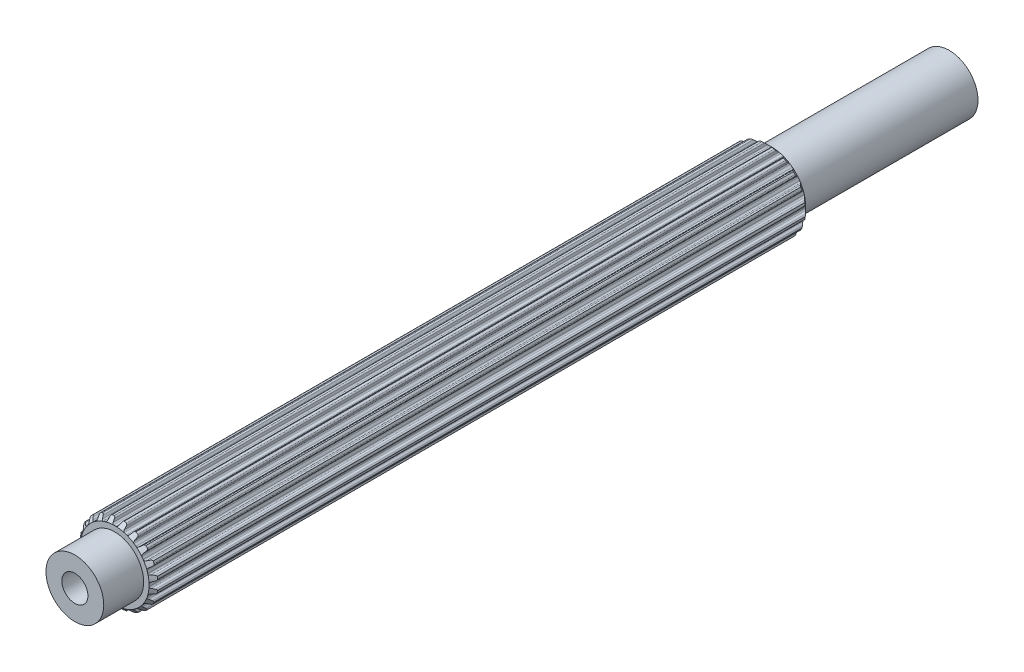
SolidWorks part; units mm, degrees
ref_plane "Front Plane" through (0, 0, 0) normal (0, 0, 1) x (1, 0, 0)
ref_plane "Top Plane" through (0, 0, 0) normal (0, 1, 0) x (1, 0, 0)
ref_plane "Right Plane" through (0, 0, 0) normal (1, 0, 0) x (0, 0, -1)
sketch "Sketch1" plane through (0, 0, 0) normal (0, 0, 1) x (1, 0, 0)
  line L0 (-0.1069, 2.9699) -> (0.1069, 2.9699)
  line L1 (0.3159, 3.2375) -> (0.2537, 3.0575)
  line L2 (-0.2964, 3.2367) -> (-0.2318, 3.0575)
  line L3 (-0.2964, 3.2367) -> (0.3159, 3.2375) construction
  line L4 (0, 3.3252) -> (0, 0) construction
  line L5 (-0.2318, 3.0575) -> (0.2537, 3.0575) construction
  line L6 (-0.4281, 3.3241) -> (0.4281, 3.3263) construction
  line L7 (0.7183, 3.1698) -> (0.7244, 2.9795)
  line L8 (0.816, 2.8576) -> (1.0195, 2.7915)
  line L9 (1.3009, 2.9815) -> (1.1862, 2.8295)
  line L10 (1.6627, 2.7927) -> (1.6097, 2.6099)
  line L11 (1.6591, 2.4655) -> (1.8322, 2.3398)
  line L12 (2.1585, 2.4335) -> (2.0025, 2.3245)
  line L13 (2.4443, 2.1423) -> (2.3374, 1.9847)
  line L14 (2.3398, 1.8322) -> (2.4655, 1.6591)
  line L15 (2.8049, 1.6474) -> (2.6228, 1.5919)
  line L16 (2.9866, 1.2821) -> (2.8363, 1.1653)
  line L17 (2.7915, 1.0195) -> (2.8576, 0.816)
  line L18 (3.1767, 0.7) -> (2.9863, 0.7035)
  line L19 (3.2367, 0.2964) -> (3.0575, 0.2318)
  line L20 (2.9699, 0.1069) -> (2.9699, -0.1069)
  line L21 (3.2375, -0.3159) -> (3.0575, -0.2537)
  line L22 (3.1698, -0.7183) -> (2.9795, -0.7244)
  line L23 (2.8576, -0.816) -> (2.7915, -1.0195)
  line L24 (2.9815, -1.3009) -> (2.8295, -1.1862)
  line L25 (2.7927, -1.6627) -> (2.6099, -1.6097)
  line L26 (2.4655, -1.6591) -> (2.3398, -1.8322)
  line L27 (2.4335, -2.1585) -> (2.3245, -2.0025)
  line L28 (2.1423, -2.4443) -> (1.9847, -2.3374)
  line L29 (1.8322, -2.3398) -> (1.6591, -2.4655)
  line L30 (1.6474, -2.8049) -> (1.5919, -2.6228)
  line L31 (1.2821, -2.9866) -> (1.1653, -2.8363)
  line L32 (1.0195, -2.7915) -> (0.816, -2.8576)
  line L33 (0.7, -3.1767) -> (0.7035, -2.9863)
  line L34 (0.2964, -3.2367) -> (0.2318, -3.0575)
  line L35 (0.1069, -2.9699) -> (-0.1069, -2.9699)
  line L36 (-0.3159, -3.2375) -> (-0.2537, -3.0575)
  line L37 (-0.7183, -3.1698) -> (-0.7244, -2.9795)
  line L38 (-0.816, -2.8576) -> (-1.0195, -2.7915)
  line L39 (-1.3009, -2.9815) -> (-1.1862, -2.8295)
  line L40 (-1.6627, -2.7927) -> (-1.6097, -2.6099)
  line L41 (-1.6591, -2.4655) -> (-1.8322, -2.3398)
  line L42 (-2.1585, -2.4335) -> (-2.0025, -2.3245)
  line L43 (-2.4443, -2.1423) -> (-2.3374, -1.9847)
  line L44 (-2.3398, -1.8322) -> (-2.4655, -1.6591)
  line L45 (-2.8049, -1.6474) -> (-2.6228, -1.5919)
  line L46 (-2.9866, -1.2821) -> (-2.8363, -1.1653)
  line L47 (-2.7915, -1.0195) -> (-2.8576, -0.816)
  line L48 (-3.1767, -0.7) -> (-2.9863, -0.7035)
  line L49 (-3.2367, -0.2964) -> (-3.0575, -0.2318)
  line L50 (-2.9699, -0.1069) -> (-2.9699, 0.1069)
  line L51 (-3.2375, 0.3159) -> (-3.0575, 0.2537)
  line L52 (-3.1698, 0.7183) -> (-2.9795, 0.7244)
  line L53 (-2.8576, 0.816) -> (-2.7915, 1.0195)
  line L54 (-2.9815, 1.3009) -> (-2.8295, 1.1862)
  line L55 (-2.7927, 1.6627) -> (-2.6099, 1.6097)
  line L56 (-2.4655, 1.6591) -> (-2.3398, 1.8322)
  line L57 (-2.4335, 2.1585) -> (-2.3245, 2.0025)
  line L58 (-2.1423, 2.4443) -> (-1.9847, 2.3374)
  line L59 (-1.8322, 2.3398) -> (-1.6591, 2.4655)
  line L60 (-1.6474, 2.8049) -> (-1.5919, 2.6228)
  line L61 (-1.2821, 2.9866) -> (-1.1653, 2.8363)
  line L62 (-1.0195, 2.7915) -> (-0.816, 2.8576)
  line L63 (-0.7, 3.1767) -> (-0.7035, 2.9863)
  line L64 (0.4281, 3.3263) -> (0.62, 3.2938)
  line L65 (1.4351, 3.0312) -> (1.6075, 2.9409)
  line L66 (2.3015, 2.4394) -> (2.4376, 2.3003)
  line L67 (2.9427, 1.6088) -> (3.0291, 1.4344)
  line L68 (3.2958, 0.6207) -> (3.3241, 0.4281)
  line L69 (3.3263, -0.4281) -> (3.2938, -0.62)
  line L70 (3.0312, -1.4351) -> (2.9409, -1.6075)
  line L71 (2.4394, -2.3015) -> (2.3003, -2.4376)
  line L72 (1.6088, -2.9427) -> (1.4344, -3.0291)
  line L73 (0.6207, -3.2958) -> (0.4281, -3.3241)
  line L74 (-0.4281, -3.3263) -> (-0.62, -3.2938)
  line L75 (-1.4351, -3.0312) -> (-1.6075, -2.9409)
  line L76 (-2.3015, -2.4394) -> (-2.4376, -2.3003)
  line L77 (-2.9427, -1.6088) -> (-3.0291, -1.4344)
  line L78 (-3.2958, -0.6207) -> (-3.3241, -0.4281)
  line L79 (-3.3263, 0.4281) -> (-3.2938, 0.62)
  line L80 (-3.0312, 1.4351) -> (-2.9409, 1.6075)
  line L81 (-2.4394, 2.3015) -> (-2.3003, 2.4376)
  line L82 (-1.6088, 2.9427) -> (-1.4344, 3.0291)
  line L83 (-0.6207, 3.2958) -> (-0.4281, 3.3241)
  arc A0 (0.2537, 3.0575) -> (0.1069, 2.9699) centre (0.1283, 3.1009) cw
  arc A1 (-0.2318, 3.0575) -> (-0.1069, 2.9699) centre (-0.1069, 3.1026) ccw
  arc A2 (0.62, 3.2938) -> (0.7183, 3.1698) centre (0.5856, 3.1656) cw
  arc A3 (0.7244, 2.9795) -> (0.816, 2.8576) centre (0.857, 2.9838) ccw
  arc A4 (-0.4281, 3.3241) -> (-0.2964, 3.2367) centre (-0.4213, 3.1916) cw
  arc A5 (0.4281, 3.3263) -> (0.3159, 3.2375) centre (0.4413, 3.1942) ccw
  arc A6 (1.1862, 2.8295) -> (1.0195, 2.7915) centre (1.0802, 2.9095) cw
  arc A7 (1.4351, 3.0312) -> (1.3009, 2.9815) centre (1.4068, 2.9015) ccw
  arc A8 (1.6075, 2.9409) -> (1.6627, 2.7927) centre (1.5352, 2.8297) cw
  arc A9 (1.6097, 2.6099) -> (1.6591, 2.4655) centre (1.7371, 2.5729) ccw
  arc A10 (2.0025, 2.3245) -> (1.8322, 2.3398) centre (1.9264, 2.4332) cw
  arc A11 (2.3015, 2.4394) -> (2.1585, 2.4335) centre (2.2346, 2.3248) ccw
  arc A12 (2.4376, 2.3003) -> (2.4443, 2.1423) centre (2.3345, 2.2168) cw
  arc A13 (2.3374, 1.9847) -> (2.3398, 1.8322) centre (2.4472, 1.9102) ccw
  arc A14 (2.6228, 1.5919) -> (2.4655, 1.6591) centre (2.5841, 1.7189) cw
  arc A15 (2.9427, 1.6088) -> (2.8049, 1.6474) centre (2.8436, 1.5205) ccw
  arc A16 (3.0291, 1.4344) -> (2.9866, 1.2821) centre (2.9052, 1.3869) cw
  arc A17 (2.8363, 1.1653) -> (2.7915, 1.0195) centre (2.9177, 1.0605) ccw
  arc A18 (2.9863, 0.7035) -> (2.8576, 0.816) centre (2.9887, 0.8362) cw
  arc A19 (3.2958, 0.6207) -> (3.1767, 0.7) centre (3.1743, 0.5673) ccw
  arc A20 (3.3241, 0.4281) -> (3.2367, 0.2964) centre (3.1916, 0.4213) cw
  arc A21 (3.0575, 0.2318) -> (2.9699, 0.1069) centre (3.1026, 0.1069) ccw
  arc A22 (3.0575, -0.2537) -> (2.9699, -0.1069) centre (3.1009, -0.1283) cw
  arc A23 (3.3263, -0.4281) -> (3.2375, -0.3159) centre (3.1942, -0.4413) ccw
  arc A24 (3.2938, -0.62) -> (3.1698, -0.7183) centre (3.1656, -0.5856) cw
  arc A25 (2.9795, -0.7244) -> (2.8576, -0.816) centre (2.9838, -0.857) ccw
  arc A26 (2.8295, -1.1862) -> (2.7915, -1.0195) centre (2.9095, -1.0802) cw
  arc A27 (3.0312, -1.4351) -> (2.9815, -1.3009) centre (2.9015, -1.4068) ccw
  arc A28 (2.9409, -1.6075) -> (2.7927, -1.6627) centre (2.8297, -1.5352) cw
  arc A29 (2.6099, -1.6097) -> (2.4655, -1.6591) centre (2.5729, -1.7371) ccw
  arc A30 (2.3245, -2.0025) -> (2.3398, -1.8322) centre (2.4332, -1.9264) cw
  arc A31 (2.4394, -2.3015) -> (2.4335, -2.1585) centre (2.3248, -2.2346) ccw
  arc A32 (2.3003, -2.4376) -> (2.1423, -2.4443) centre (2.2168, -2.3345) cw
  arc A33 (1.9847, -2.3374) -> (1.8322, -2.3398) centre (1.9102, -2.4472) ccw
  arc A34 (1.5919, -2.6228) -> (1.6591, -2.4655) centre (1.7189, -2.5841) cw
  arc A35 (1.6088, -2.9427) -> (1.6474, -2.8049) centre (1.5205, -2.8436) ccw
  arc A36 (1.4344, -3.0291) -> (1.2821, -2.9866) centre (1.3869, -2.9052) cw
  arc A37 (1.1653, -2.8363) -> (1.0195, -2.7915) centre (1.0605, -2.9177) ccw
  arc A38 (0.7035, -2.9863) -> (0.816, -2.8576) centre (0.8362, -2.9887) cw
  arc A39 (0.6207, -3.2958) -> (0.7, -3.1767) centre (0.5673, -3.1743) ccw
  arc A40 (0.4281, -3.3241) -> (0.2964, -3.2367) centre (0.4213, -3.1916) cw
  arc A41 (0.2318, -3.0575) -> (0.1069, -2.9699) centre (0.1069, -3.1026) ccw
  arc A42 (-0.2537, -3.0575) -> (-0.1069, -2.9699) centre (-0.1283, -3.1009) cw
  arc A43 (-0.4281, -3.3263) -> (-0.3159, -3.2375) centre (-0.4413, -3.1942) ccw
  arc A44 (-0.62, -3.2938) -> (-0.7183, -3.1698) centre (-0.5856, -3.1656) cw
  arc A45 (-0.7244, -2.9795) -> (-0.816, -2.8576) centre (-0.857, -2.9838) ccw
  arc A46 (-1.1862, -2.8295) -> (-1.0195, -2.7915) centre (-1.0802, -2.9095) cw
  arc A47 (-1.4351, -3.0312) -> (-1.3009, -2.9815) centre (-1.4068, -2.9015) ccw
  arc A48 (-1.6075, -2.9409) -> (-1.6627, -2.7927) centre (-1.5352, -2.8297) cw
  arc A49 (-1.6097, -2.6099) -> (-1.6591, -2.4655) centre (-1.7371, -2.5729) ccw
  arc A50 (-2.0025, -2.3245) -> (-1.8322, -2.3398) centre (-1.9264, -2.4332) cw
  arc A51 (-2.3015, -2.4394) -> (-2.1585, -2.4335) centre (-2.2346, -2.3248) ccw
  arc A52 (-2.4376, -2.3003) -> (-2.4443, -2.1423) centre (-2.3345, -2.2168) cw
  arc A53 (-2.3374, -1.9847) -> (-2.3398, -1.8322) centre (-2.4472, -1.9102) ccw
  arc A54 (-2.6228, -1.5919) -> (-2.4655, -1.6591) centre (-2.5841, -1.7189) cw
  arc A55 (-2.9427, -1.6088) -> (-2.8049, -1.6474) centre (-2.8436, -1.5205) ccw
  arc A56 (-3.0291, -1.4344) -> (-2.9866, -1.2821) centre (-2.9052, -1.3869) cw
  arc A57 (-2.8363, -1.1653) -> (-2.7915, -1.0195) centre (-2.9177, -1.0605) ccw
  arc A58 (-2.9863, -0.7035) -> (-2.8576, -0.816) centre (-2.9887, -0.8362) cw
  arc A59 (-3.2958, -0.6207) -> (-3.1767, -0.7) centre (-3.1743, -0.5673) ccw
  arc A60 (-3.3241, -0.4281) -> (-3.2367, -0.2964) centre (-3.1916, -0.4213) cw
  arc A61 (-3.0575, -0.2318) -> (-2.9699, -0.1069) centre (-3.1026, -0.1069) ccw
  arc A62 (-3.0575, 0.2537) -> (-2.9699, 0.1069) centre (-3.1009, 0.1283) cw
  arc A63 (-3.3263, 0.4281) -> (-3.2375, 0.3159) centre (-3.1942, 0.4413) ccw
  arc A64 (-3.2938, 0.62) -> (-3.1698, 0.7183) centre (-3.1656, 0.5856) cw
  arc A65 (-2.9795, 0.7244) -> (-2.8576, 0.816) centre (-2.9838, 0.857) ccw
  arc A66 (-2.8295, 1.1862) -> (-2.7915, 1.0195) centre (-2.9095, 1.0802) cw
  arc A67 (-3.0312, 1.4351) -> (-2.9815, 1.3009) centre (-2.9015, 1.4068) ccw
  arc A68 (-2.9409, 1.6075) -> (-2.7927, 1.6627) centre (-2.8297, 1.5352) cw
  arc A69 (-2.6099, 1.6097) -> (-2.4655, 1.6591) centre (-2.5729, 1.7371) ccw
  arc A70 (-2.3245, 2.0025) -> (-2.3398, 1.8322) centre (-2.4332, 1.9264) cw
  arc A71 (-2.4394, 2.3015) -> (-2.4335, 2.1585) centre (-2.3248, 2.2346) ccw
  arc A72 (-2.3003, 2.4376) -> (-2.1423, 2.4443) centre (-2.2168, 2.3345) cw
  arc A73 (-1.9847, 2.3374) -> (-1.8322, 2.3398) centre (-1.9102, 2.4472) ccw
  arc A74 (-1.5919, 2.6228) -> (-1.6591, 2.4655) centre (-1.7189, 2.5841) cw
  arc A75 (-1.6088, 2.9427) -> (-1.6474, 2.8049) centre (-1.5205, 2.8436) ccw
  arc A76 (-1.4344, 3.0291) -> (-1.2821, 2.9866) centre (-1.3869, 2.9052) cw
  arc A77 (-1.1653, 2.8363) -> (-1.0195, 2.7915) centre (-1.0605, 2.9177) ccw
  arc A78 (-0.7035, 2.9863) -> (-0.816, 2.8576) centre (-0.8362, 2.9887) cw
  arc A79 (-0.6207, 3.2958) -> (-0.7, 3.1767) centre (-0.5673, 3.1743) ccw
  point P14 (0, 2.9699)
  point P247 (0, 0)
  dimension "D4" = 0.1327
  dimension "D8" = 20
  dimension "D1" = 2.9699
  dimension "D2" = 0.2139
  dimension "D3" = 0.1904
  dimension "D5" = 0.0877
  dimension "D6" = 0.4855
  dimension "D7" = 0.8563
extrude "Boss-Extrude1" add sketch "Sketch1" along normal blind 34.3751 and the other way blind 22.4371
sketch "Sketch2" plane through (0, 0, 0) normal (0, 0, 1) x (1, 0, 0)
  circle A0 centre (0, 0) radius 2.5019
  dimension "D1" = 5.0038
extrude "Boss-Extrude2" add sketch "Sketch2" along normal mid plane 75.659
sketch "Sketch4" plane through (0, 0, 37.8295) normal (0, 0, 1) x (1, 0, 0)
  circle A0 centre (0, 0) radius 2.5019 construction
  point P0 (0, 0)
sketch "Sketch5" plane through (0, 0, -37.8295) normal (0, 0, -1) x (-1, 0, 0)
  circle A0 centre (0, 0) radius 2.5019 construction
  point P0 (0, 0)
sketch "Sketch3" plane through (0, 0, 0) normal (1, 0, 0) x (0, 0, -1)
  line L0 (-33.2439, 4.1011) -> (-34.3751, 2.9699)
  line L1 (-34.3751, 2.9699) -> (-34.3751, 4.1011)
  line L2 (-34.3751, 4.1011) -> (-33.2439, 4.1011)
  line L3 (-34.3751, 2.5019) -> (-34.3751, -2.5019) construction
  line L5 (-14.3608, 0) -> (13.2171, 0) construction
  line L7 (22.4371, 19.151) -> (22.4371, 2.9699)
  line L8 (22.4371, 2.9699) -> (14.3465, 11.0604)
  line L9 (14.3465, 11.0604) -> (22.4371, 19.151)
  line L10 (22.4371, -2.5019) -> (22.4371, 2.5019) construction
  point P6 (-4.866, 6.1438)
  dimension "D1" = 45
  dimension "D2" = 45
revolve "Cut-Revolve1" cut sketch "Sketch3" angle 360 about L5
sketch "Sketch7" plane through (0, 0, 0) normal (0, 0, 1) x (1, 0, 0)
  circle A0 centre (0, 0) radius 1.1303
  dimension "D1" = 2.2606
extrude "Cut-Extrude1" cut sketch "Sketch7" along normal up to surface and the other way up to surface up to face at (2.5019, 0, 37.8295) other way up to face at (2.5019, 0, -37.8295)
sketch "Sketch8" plane through (0, 0, 0) normal (0, 0, 1) x (1, 0, 0)
  circle A0 centre (0, 0) radius 1.1303
  circle A1 centre (0, 0) radius 1.1303 construction
extrude "Boss-Extrude3" add sketch "Sketch8" along normal offset from surface 9.525 and the other way offset from surface (28.3045 mm away) 9.525 up to face at (1.1303, 0, 37.8295) other way up to face at (1.1303, 0, -37.8295)
